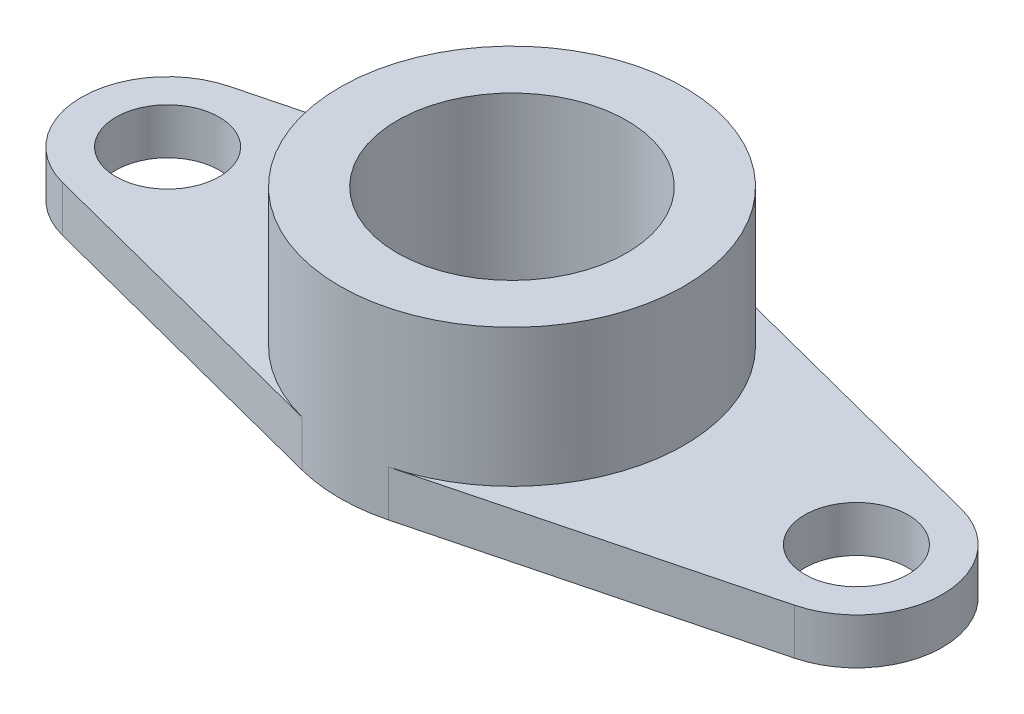
SolidWorks part; units mm, degrees
ref_plane "Front Plane" through (0, 0, 0) normal (0, 0, 1) x (1, 0, 0)
ref_plane "Top Plane" through (0, 0, 0) normal (0, 1, 0) x (1, 0, 0)
ref_plane "Right Plane" through (0, 0, 0) normal (1, 0, 0) x (0, 0, -1)
sketch "Sketch2" plane through (0, 0, 0) normal (0, 1, 0) x (1, 0, 0)
  line L0 (-15.9375, 3.6309) -> (-1.875, 7.2618)
  line L1 (15.9375, 3.6309) -> (1.875, 7.2618)
  line L2 (-15.9375, -3.6309) -> (-1.875, -7.2618)
  line L3 (15.9375, -3.6309) -> (1.875, -7.2618)
  circle A0 centre (0, 0) radius 7.5
  circle A1 centre (-15, 0) radius 3.75
  circle A2 centre (15, 0) radius 3.75
  circle A3 centre (-15, 0) radius 2.25
  circle A4 centre (15, 0) radius 2.25
  circle A5 centre (0, 0) radius 5
  dimension "D1" = 15
  dimension "D2" = 7.5
  dimension "D3" = 7.5
  dimension "D6" = 10
  dimension "D7" = 4.5
  dimension "D8" = 4.5
  dimension "D4" = 15
  dimension "D5" = 15
extrude "Boss-Extrude2" add sketch "Sketch2" along normal blind 2 contours A1 A3 | A1 L2 A0 L0 | A0 A5 | A2 L1 A0 L3 | A2 A4
sketch "Sketch3" plane through (0, 2, 0) normal (0, 1, 0) x (1, 0, 0)
  circle A0 centre (0, 0) radius 7.5
  circle A1 centre (0, 0) radius 5
  dimension "D1" = 15
extrude "Boss-Extrude3" add sketch "Sketch3" along normal blind 6
equation "\"D2@Sketch2\"=3.75*2"
equation "\"D3@Sketch2\"=3.75*2"
